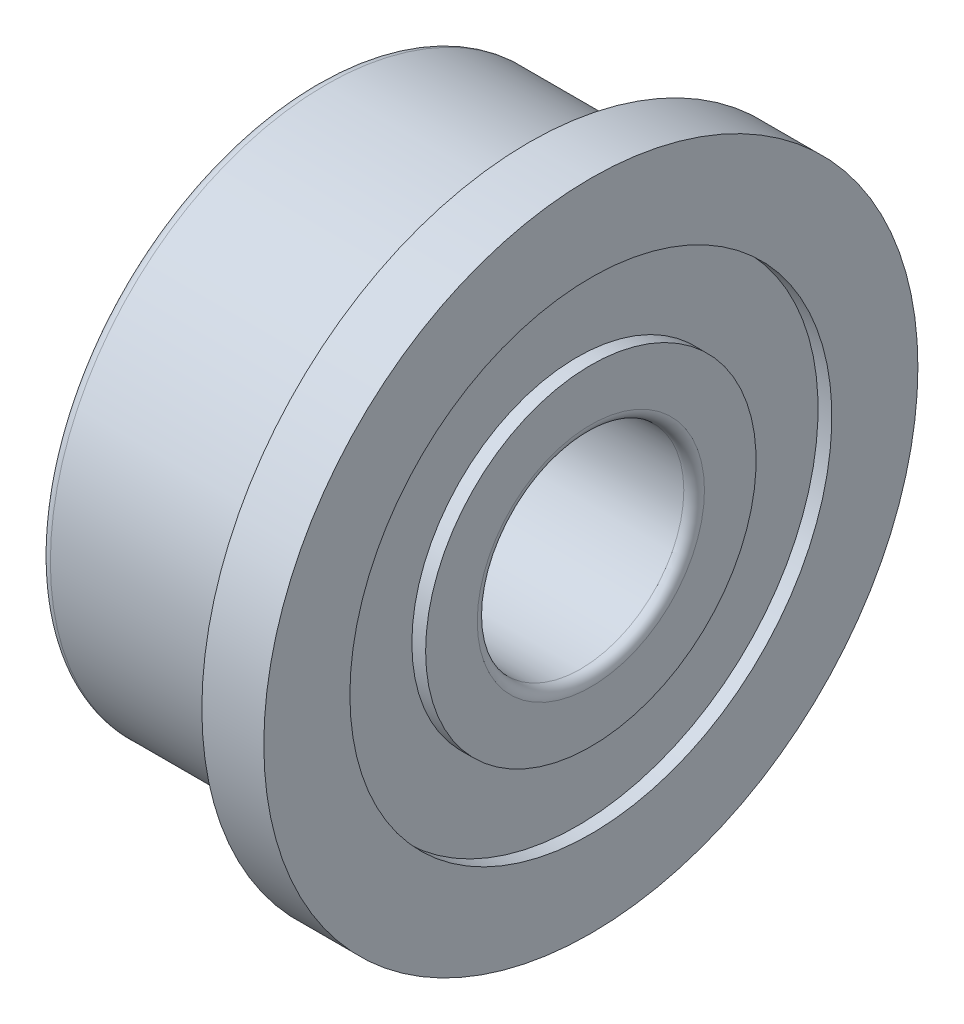
SolidWorks part; units mm, degrees
ref_plane "Front Plane" through (0, 0, 0) normal (0, 0, 1) x (1, 0, 0)
ref_plane "Top Plane" through (0, 0, 0) normal (0, 1, 0) x (1, 0, 0)
ref_plane "Right Plane" through (0, 0, 0) normal (1, 0, 0) x (0, 0, -1)
sketch "Sketch1" plane through (0, 0, 0) normal (0, 0, 1) x (1, 0, 0)
  line L0 (-3.1, 0) -> (0.9, 0) construction
  line L1 (0, 4.2) -> (0, 4.75)
  line L2 (0, 4.75) -> (0.9, 4.75)
  line L3 (0.9, 4.75) -> (0.9, 3.5)
  line L4 (0.9, 1.5) -> (-3.1, 1.5)
  line L5 (-3.1, 1.5) -> (-3.1, 2.4)
  line L6 (-3.1, 4) -> (-0.2, 4)
  line L7 (-3.1, 3.5) -> (-2.9, 3.5)
  line L8 (-2.9, 3.5) -> (-2.9, 2.4)
  line L9 (-2.9, 2.4) -> (-3.1, 2.4)
  line L10 (0.9, 3.5) -> (0.7, 3.5)
  line L11 (0.7, 3.5) -> (0.7, 2.4)
  line L12 (0.7, 2.4) -> (0.9, 2.4)
  line L13 (-3.1, 3.5) -> (-3.1, 4)
  line L14 (0.9, 2.4) -> (0.9, 1.5)
  arc A0 (-0.2, 4) -> (0, 4.2) centre (0, 4) ccw
  dimension "FIX_1" = 0.2
  dimension "D_s" = 3
  dimension "C" = 0.9
  dimension "MSM_2" = 4.8
  dimension "MSM_1" = 7
  dimension "D" = 8
  dimension "D1." = 9.5
  dimension "B" = 4
  dimension "MSM_3" = 0.2
revolve "Revolve1" add sketch "Sketch1" angle 360 about L0
fillet "Fillet1" radius 0.15 3 edges at (0.9, 0, 1.5) (-3.1, 0, 1.5) (-3.1, 0, 4)
